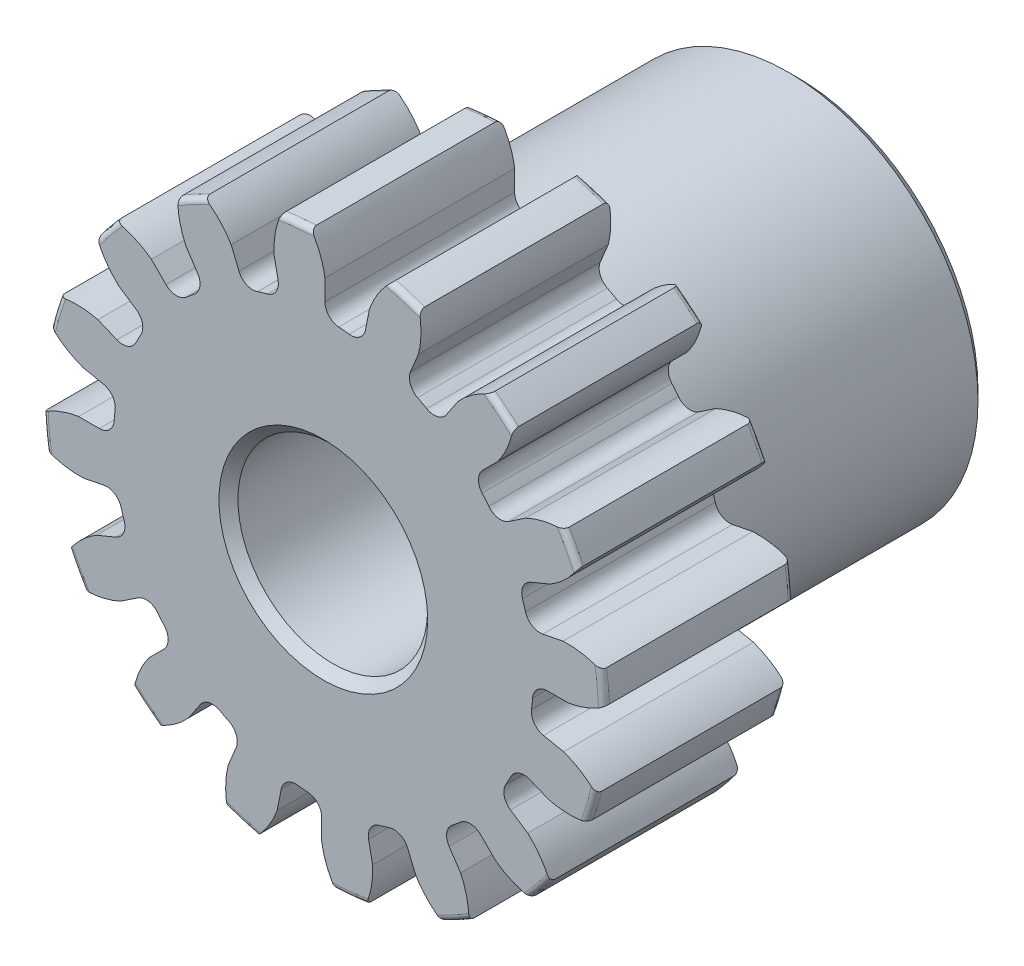
SolidWorks part; units mm, degrees
ref_plane "Front" through (0, 0, 0) normal (0, 0, 1) x (1, 0, 0)
ref_plane "Top" through (0, 0, 0) normal (0, 1, 0) x (1, 0, 0)
ref_plane "Right" through (0, 0, 0) normal (1, 0, 0) x (0, 0, -1)
sketch "Sketch1" plane through (0, 0, 0) normal (0, 0, 1) x (1, 0, 0)
  line L0 (-203.2, 0) -> (203.2, 0) construction
  circle A0 centre (0, 0) radius 4.699
  circle A1 centre (0, 0) radius 4.2291 construction
  circle A3 centre (0, 0) radius 3.5096 construction
  dimension "D1" = 1.1894
  dimension "OD" = 9.398
  dimension "Ptich Dia" = 8.4582
  dimension "Root Dia" = 7.0191
  dimension "D3" = 0.4699
  dimension "Number of Teeth" = 406.4
extrude "Boss-Extrude1" add sketch "Sketch1" against normal blind 3.175
sketch "Sketch2" plane through (0, 0, 0) normal (1, 0, 0) x (0, 0, -1)
  line L0 (3.175, 0) -> (7.9375, 0)
  line L1 (3.175, 0) -> (3.175, 3.175)
  line L2 (3.175, 3.175) -> (7.9375, 3.175)
  line L3 (7.9375, 3.175) -> (7.9375, 0)
  point P5 (7.9375, -3.175)
  point P6 (0, -4.699)
  point P7 (3.175, -4.699)
  point P9 (0, 4.699)
  dimension "Face Wd" = 3.175
  dimension "B Hub Dia" = 6.35
  dimension "D O'all Lg." = 7.9375
revolve "Revolve1" add sketch "Sketch2" angle 360 about L0
fillet "Fillet2" radius 0.094 3 edges at (4.699, 0, -3.175) (4.699, 0, 0) (3.175, 0, -3.175)
sketch "Sketch3" plane through (0, 0, 0) normal (0, 0, 1) x (1, 0, 0)
  line L0 (0, 0) -> (0, 4.699) construction
  line L1 (-1.0252, 3.964) -> (0, 4.2291)
  line L2 (-9.5921, 4.2291) -> (9.5921, 4.2291) construction
  line L3 (-9.2865, 1.8274) -> (9.2865, 6.6308) construction
  line L4 (-1.0252, 3.964) -> (0, 0) construction
  line L5 (-2.6148, 3.1507) -> (0, 0) construction
  line L6 (-2.6148, 3.1507) -> (-0.4344, 4.9603) construction
  line L7 (-0.7148, 4.0315) -> (0, 0) construction
  line L8 (-0.7148, 4.0315) -> (0.015, 4.1609) construction
  arc A0 (-1.0252, 3.964) -> (-2.6148, 3.1507) centre (0, 0) ccw
  circle A1 centre (0, 0) radius 4.2291 construction
  circle A2 centre (0, 0) radius 4.0944 construction
  arc A3 (-1.0252, 3.964) -> (-0.7148, 4.0315) centre (0, 0) cw
  circle A4 centre (0, 0) radius 4.699 construction
  point P6 (0, 4.2291)
  dimension "D1" = 1.0589
  dimension "Pressure Angle" = 14.5
  dimension "D2" = 1.8001
  dimension "D3" = 2.8336
  dimension "D4" = 0.3177
  dimension "D5" = 0.7412
sketch "Sketch4" plane through (0, 0, 0) normal (0, 0, 1) x (1, 0, 0)
  line L0 (0, 0) -> (0.4125, 4.1885) construction
  line L1 (0.0264, 4.0943) -> (0.0264, 3.5095)
  line L2 (0, 4.2291) -> (0.8251, 4.1478) construction
  line L3 (0.7729, 4.0208) -> (0.6588, 3.4472)
  line L4 (0.0264, 3.5095) -> (0, 0) construction
  line L5 (0, 0) -> (0, 4.699) construction
  line L6 (-2.6148, 3.1507) -> (-0.4344, 4.9603) construction
  line L7 (-2.6148, 3.1507) -> (-0.4344, 4.9603) construction
  arc A0 (0.6588, 3.4472) -> (0.0264, 3.5095) centre (0, 0) ccw
  arc A1 (0, 4.2291) -> (0.8251, 4.1478) centre (0, 0) cw construction
  circle A2 centre (0, 0) radius 4.2291 construction
  circle A3 centre (0, 0) radius 4.0944 construction
  circle A4 centre (0, 0) radius 3.5096 construction
  arc A5 (1.3937, 4.7803) -> (-0.4344, 4.9603) centre (0, 0) ccw
  spline S0 degree 2 poles (-0.4344, 4.9603) (-0.0456, 4.5834) (0.0264, 4.0943) knots 0 0 0 1 1 1
  spline S1 degree 2 poles (1.3937, 4.7803) (0.9389, 4.4865) (0.7729, 4.0208) knots 0 0 0 1 1 1
  dimension "D1" = 0.8304
extrude "Cut-Extrude1" cut sketch "Sketch4" against normal through all
fillet "Fillet1" radius 0.2491 2 edges at (0.6588, 3.4472, -1.5875) (0.0264, 3.5095, -1.5875)
pattern_circular "CirPattern1" count 16 over 360 about axis through (0, 0, -3.175) along (0, 0, 1) of "Cut-Extrude1", "Fillet1"
sketch "Sketch5" plane through (0, 0, 0) normal (0, 0, 1) x (1, 0, 0)
  circle A0 centre (0, 0) radius 1.5875
  circle A1 centre (0, 0) radius 1.5875 construction
  dimension "Bore Min" = 3.175
  dimension "Bore Max" = 3.175
extrude "Cut-Extrude2" cut sketch "Sketch5" against normal through all
chamfer "Chamfer1" distance 0.1588 angle 45 3 edges at (3.175, 0, -7.9375) (1.5875, 0, 0) (1.5875, 0, -7.9375)
sketch "Pitch Dia" plane through (0, 0, 0) normal (0, 0, 1) x (1, 0, 0)
  circle A0 centre (0, 0) radius 4.2291 construction
  circle A1 centre (0, 0) radius 4.2291 construction
equation "\"D1@Boss-Extrude1\" = \"Face Wd@Sketch2\""
equation "\"D2@Sketch3\" = \"D1@Sketch3\"*1.7"
equation "\"D3@Sketch3\" = \"D1@Sketch3\"+\"D2@Sketch3\"-.001"
equation "\"D4@Sketch3\" = \"D1@Sketch3\"*.3"
equation "\"D5@Sketch3\" = \"D1@Sketch3\"-\"D4@Sketch3\""
equation "\"D1@Sketch4\" = 1.5708/(\"Number of Teeth@Sketch1\"/\"Ptich Dia@Sketch1\")"
equation "\"D1@Chamfer1\" = \"B Hub Dia@Sketch2\"*.025"
equation "\"D1@CirPattern1\" = \"Number of Teeth@Sketch1\""
equation "\"D1@Fillet1\" = \"D1@Sketch4\"*.3"
equation "\"D1@Fillet2\" = \"OD@Sketch1\"*.01"
equation "\"D1@Sketch1\" = 2.250/(\"Number of Teeth@Sketch1\"/\"Ptich Dia@Sketch1\")"
